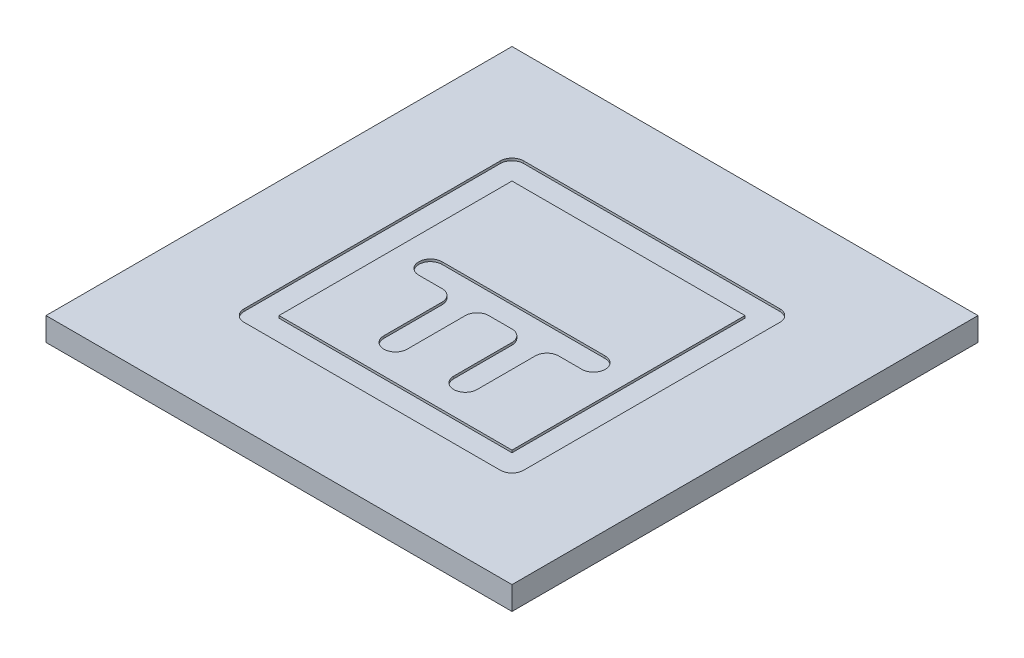
SolidWorks part; units mm, degrees
ref_plane "Front Plane" through (0, 0, 0) normal (0, 0, 1) x (1, 0, 0)
ref_plane "Top Plane" through (0, 0, 0) normal (0, 1, 0) x (1, 0, 0)
ref_plane "Right Plane" through (0, 0, 0) normal (1, 0, 0) x (0, 0, -1)
sketch "Sketch1" plane through (0, 0, 0) normal (0, 1, 0) x (1, 0, 0)
  line L1 (100, -100) -> (-100, -100)
  line L2 (100, -100) -> (100, 100)
  line L3 (100, 100) -> (-100, 100)
  line L4 (-100, -100) -> (-100, 100)
  line L5 (100, -100) -> (-100, 100) construction
  line L6 (100, 100) -> (-100, -100) construction
  point P0 (0, 0)
  dimension "D1" = 200
  dimension "D2" = 200
extrude "Boss-Extrude1" add sketch "Sketch1" along normal blind 10
sketch "Sketch2" plane through (0, 10, 0) normal (0, 1, 0) x (1, 0, 0)
  line L0 (-60, 0) -> (60, 0) construction
  line L1 (60, -60) -> (-60, -60)
  line L2 (60, -60) -> (60, 60)
  line L3 (60, 60) -> (-60, 60)
  line L4 (-60, -60) -> (-60, 60)
  line L5 (60, -60) -> (-60, 60) construction
  line L6 (60, 60) -> (-60, -60) construction
  line L7 (35, 0) -> (-35, 0) construction
  line L8 (35, -5) -> (-35, -5) construction
  line L9 (35, 5) -> (-35, 5) construction
  line L10 (0, 0) -> (0, -35) construction
  line L11 (-15, -35) -> (15, -35) construction
  line L12 (-15, -35) -> (-15, 0) construction
  line L13 (-20, -35) -> (-20, 0) construction
  line L14 (-10, -35) -> (-10, 0) construction
  line L15 (15, -35) -> (15, 0) construction
  line L16 (10, -35) -> (10, 0) construction
  line L17 (20, -35) -> (20, 0) construction
  line L18 (-35, 5) -> (35, 5)
  line L19 (50, -50) -> (-50, -50)
  line L20 (50, -50) -> (50, 50)
  line L21 (50, 50) -> (-50, 50)
  line L22 (-50, -50) -> (-50, 50)
  line L23 (50, -50) -> (-50, 50) construction
  line L24 (50, 50) -> (-50, -50) construction
  line L25 (-35, -5) -> (-35.0221, -5.0874)
  line L26 (35, -5) -> (20, -5)
  line L27 (20, -5) -> (20, -35)
  line L28 (-10, -5) -> (10, -5)
  line L29 (10, -5) -> (10, -35)
  line L30 (-35, -5) -> (-20, -5)
  line L32 (-20, -5) -> (-20, -35)
  line L33 (-10, -5) -> (-10, -35)
  arc A0 (35, -5) -> (35, 5) centre (35, 0) ccw construction
  arc A1 (-35, 5) -> (-35, -5) centre (-35, 0) ccw construction
  arc A2 (-20, -35) -> (-10, -35) centre (-15, -35) ccw construction
  arc A3 (-10, 0) -> (-20, 0) centre (-15, 0) ccw construction
  arc A4 (10, -35) -> (20, -35) centre (15, -35) ccw construction
  arc A5 (20, 0) -> (10, 0) centre (15, 0) ccw construction
  arc A6 (-20, -35) -> (-10, -35) centre (-15, -35) ccw
  arc A7 (10, -35) -> (20, -35) centre (15, -35) ccw
  arc A8 (35, -5) -> (35, 5) centre (35, 0) ccw
  arc A9 (-35, 5) -> (-35, -5) centre (-35, 0) ccw
  point P0 (0, 0)
  point P10 (0, 0)
  point P19 (0, -35)
  point P20 (-15, -17.5)
  point P26 (15, -17.5)
  dimension "D2" = 5
  dimension "D1" = 120
  dimension "D3" = 70
  dimension "D4" = 30
  dimension "D5" = 10
  dimension "D6" = 15
extrude "Cut-Extrude1" cut sketch "Sketch2" against normal blind 1 contours L18 A9 L30 L32 A6 L33 L28 L29 A7 L27 L26 A8 | L4 L1 L2 L3 L19 L22 L21 L20
fillet "Fillet1" radius 5 8 edges at (-10, 9.5, 5) (10, 9.5, 5) (20, 9.5, 5) (-20, 9.5, 5) (-60, 9.5, 60) (60, 9.5, 60) (60, 9.5, -60) (-60, 9.5, -60)
